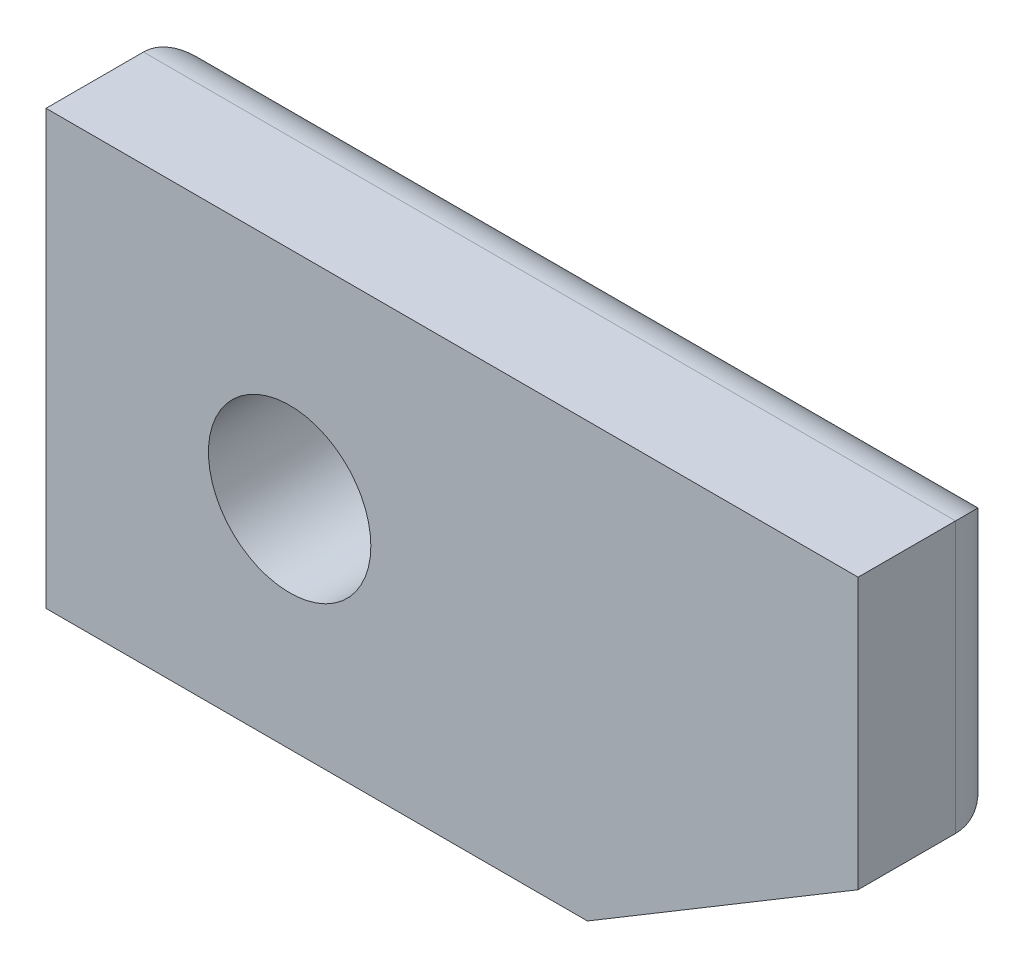
SolidWorks part; units mm, degrees
ref_plane "Front Plane" through (0, 0, 0) normal (0, 0, 1) x (1, 0, 0)
ref_plane "Top Plane" through (0, 0, 0) normal (0, 1, 0) x (1, 0, 0)
ref_plane "Right Plane" through (0, 0, 0) normal (1, 0, 0) x (0, 0, -1)
sketch "Sketch1" plane through (0, 0, 0) normal (0, 0, 1) x (1, 0, 0)
  line L0 (-2.25, 2) -> (-2.25, -2)
  line L1 (-2.25, -2) -> (2.75, -2)
  line L2 (2.75, -2) -> (5.25, -0.5)
  line L3 (5.25, -0.5) -> (5.25, 2)
  line L4 (5.25, 2) -> (-2.25, 2)
  line L5 (-2.25, 0) -> (0, 0) construction
  line L6 (0, 0.75) -> (0, 2) construction
  line L7 (2.75, -2) -> (2.75, 2) construction
  circle A0 centre (0, 0) radius 0.75
  point P11 (-0.75, 0)
  point P12 (0.75, 0)
  dimension "D1" = 1.5
  dimension "D2" = 4
  dimension "D3" = 7.5
  dimension "D4" = 1.5
  dimension "D5" = 2.25
  dimension "D6" = 4.5
  dimension "D7" = 2.5
  dimension "D8" = 5
extrude "Boss-Extrude1" add sketch "Sketch1" along normal blind 1.4
fillet "Fillet1" radius 0.5 5 edges at (-2.25, 0, 0) (0.25, -2, 0) (4, -1.25, 0) (5.25, 0.75, 0) (1.5, 2, 0)
